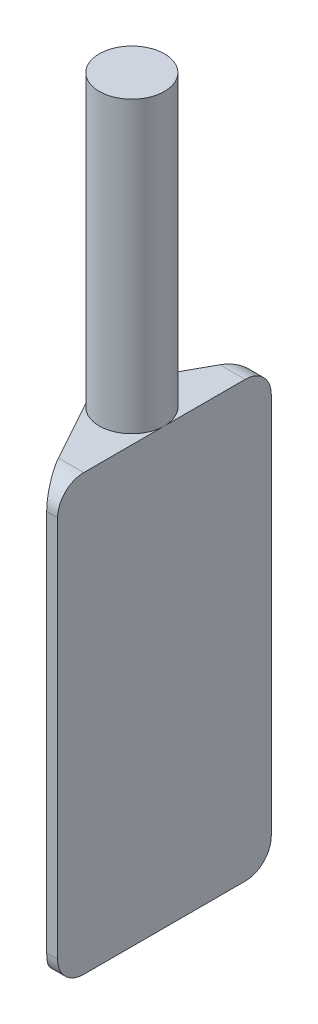
SolidWorks part; units mm, degrees
ref_plane "Alzado" through (0, 0, 0) normal (0, 0, 1) x (1, 0, 0)
ref_plane "Planta" through (0, 0, 0) normal (0, 1, 0) x (1, 0, 0)
ref_plane "Vista lateral" through (0, 0, 0) normal (1, 0, 0) x (0, 0, -1)
sketch "Croquis1" plane through (0, 0, 0) normal (0, 1, 0) x (1, 0, 0)
  circle A0 centre (0, 0) radius 9
  dimension "D1" = 18
extrude "Saliente-Extruir1" add sketch "Croquis1" along normal blind 200
sketch "Croquis2" plane through (0, 0, 0) normal (0, -1, 0) x (1, 0, 0)
  line L0 (6, 29.5) -> (-7.8798, 4.3484)
  line L1 (6, 29.5) -> (9, 29.5)
  line L3 (6, -29.5) -> (9, -29.5)
  line L4 (9, 29.5) -> (9, -29.5)
  line L5 (6, -29.5) -> (-7.8798, -4.3484)
  circle A0 centre (0, 0) radius 9 construction
  arc A1 (-7.8798, 4.3484) -> (-7.8798, -4.3484) centre (0, 0) ccw
  point P6 (9, 0)
  dimension "D1" = 59
  dimension "D2" = 3
extrude "Saliente-Extruir2" add sketch "Croquis2" against normal blind 120
fillet "Redondeo1" radius 7.2 4 edges at (7.5, 0, 29.5) (7.5, 120, 29.5) (7.5, 0, -29.5) (7.5, 120, -29.5)
sketch "Croquis3" plane through (0, 0, -29.5) normal (0, 0, -1) x (-1, 0, 0)
  line L0 (-2.0267, 0) -> (10.6568, 15.1156)
  line L1 (10.6568, 15.1156) -> (12.9075, -4.5435)
  line L2 (12.9075, -4.5435) -> (-2.0267, 0)
  line L3 (7.8798, 0) -> (-2.0267, 0) construction
  point P6 (10.6568, 15.1156)
  dimension "D1" = 50
extrude "Cortar-Extruir1" cut sketch "Croquis3" against normal blind 120
